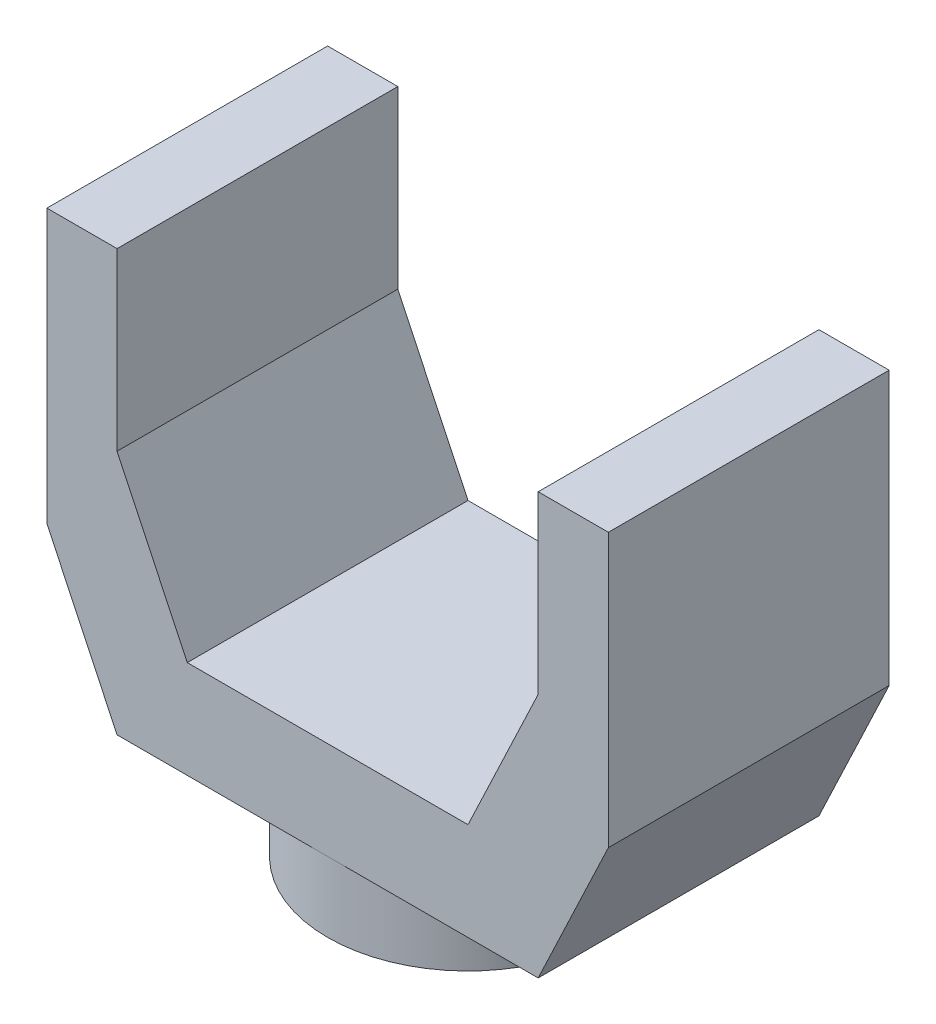
SolidWorks part; units mm, degrees
ref_plane "Front Plane" through (0, 0, 0) normal (0, 0, 1) x (1, 0, 0)
ref_plane "Top Plane" through (0, 0, 0) normal (0, 1, 0) x (1, 0, 0)
ref_plane "Right Plane" through (0, 0, 0) normal (1, 0, 0) x (0, 0, -1)
sketch "Sketch1" plane through (0, 0, 0) normal (0, 0, 1) x (1, 0, 0)
  line L0 (-38.1, 0) -> (38.1, 0)
  line L1 (38.1, 0) -> (50.8, 26.774)
  line L2 (50.8, 26.774) -> (50.8, 76.2)
  line L3 (50.8, 76.2) -> (38.1, 76.2)
  line L4 (38.1, 76.2) -> (38.1, 44.45)
  line L5 (38.1, 44.45) -> (25.4, 17.676)
  line L6 (25.4, 17.676) -> (-25.4, 17.676)
  line L7 (0, -55) -> (0, 55) construction
  line L8 (-38.1, 0) -> (-50.8, 26.774)
  line L9 (-50.8, 26.774) -> (-50.8, 76.2)
  line L10 (-50.8, 76.2) -> (-38.1, 76.2)
  line L11 (-38.1, 76.2) -> (-38.1, 44.45)
  line L12 (-38.1, 44.45) -> (-25.4, 17.676)
  point P4 (0, 0)
  point P18 (0, 17.676)
  dimension "D1" = 76.2
  dimension "D2" = 12.7
  dimension "D3" = 76.2
  dimension "D4" = 19.05
  dimension "D5" = 50.8
  dimension "D6" = 76.2
  dimension "D7" = 31.75
extrude "Boss-Extrude1" add sketch "Sketch1" along normal mid plane 50.8
sketch "Sketch2" plane through (0, 0, 0) normal (0, -1, 0) x (1, 0, 0)
  circle A0 centre (0, 0) radius 25.4
  dimension "D1" = 50.8
extrude "Boss-Extrude2" add sketch "Sketch2" along normal blind 12.7
